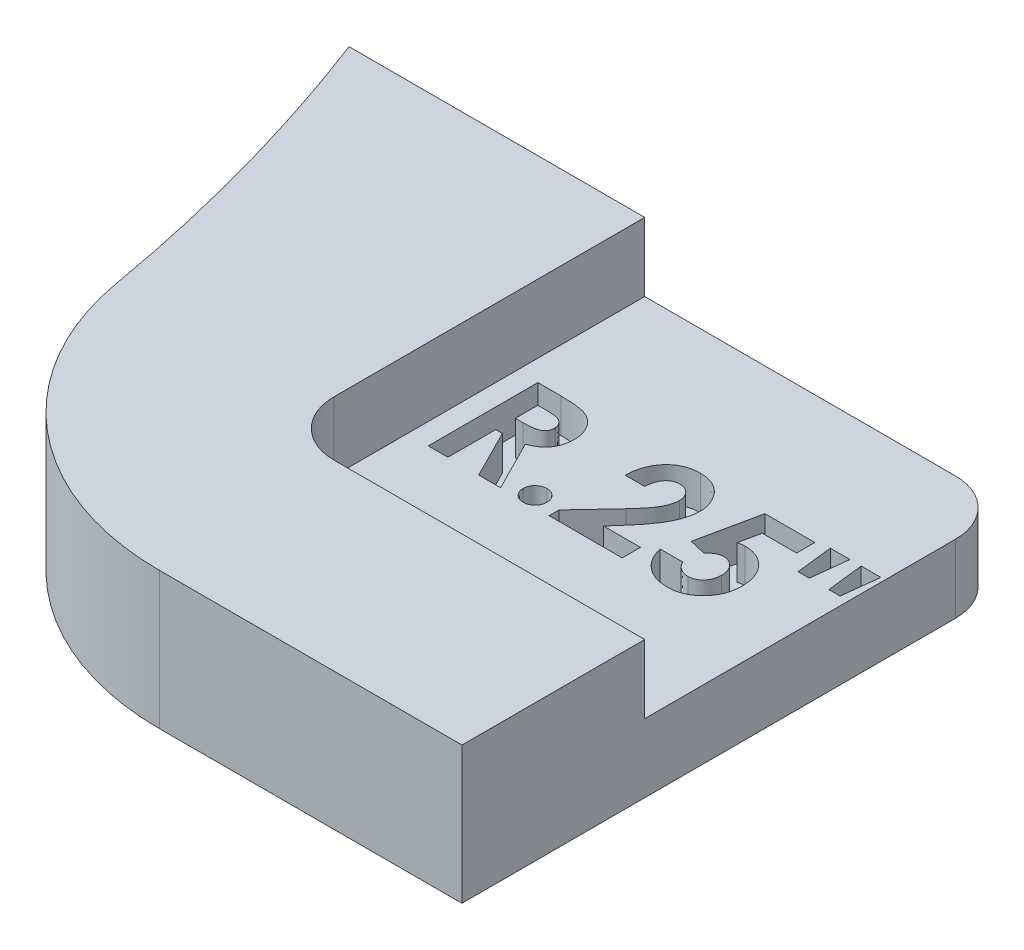
SolidWorks part; units mm, degrees
ref_plane "Front Plane" through (0, 0, 0) normal (0, 0, 1) x (1, 0, 0)
ref_plane "Top Plane" through (0, 0, 0) normal (0, 1, 0) x (1, 0, 0)
ref_plane "Right Plane" through (0, 0, 0) normal (1, 0, 0) x (0, 0, -1)
sketch "Sketch2" plane through (0, 0, 0) normal (0, 1, 0) x (1, 0, 0)
  line L0 (39.9034, 0) -> (66.5271, 0) construction
  line L4 (39.8718, 1.5875) -> (52.5718, 1.5875)
  line L5 (52.5718, 1.5875) -> (52.5718, 14.2875)
  line L6 (52.5718, 14.2875) -> (37.2579, 14.2875)
  arc A0 (39.8718, 1.5875) -> (37.2579, 14.2875) centre (0, 0) ccw
  arc A1 (37.2579, 14.2875) -> (-39.9034, 0) centre (0, 0) ccw construction
  arc A2 (-39.9034, 0) -> (39.9034, 0) centre (0, 0) ccw construction
  arc A3 (39.9034, 0) -> (39.8718, 1.5875) centre (0, 0) ccw construction
  point P6 (45.8249, 5.2638)
  point P7 (37.9479, 12.3384)
  point P10 (43.0639, 5.8161)
extrude "Boss-Extrude1" add sketch "Sketch2" along normal mid plane 3.175
fillet "Fillet1" radius 6.35 1 edges at (39.8718, 0, -1.5875)
sketch "Sketch3" plane through (0, 1.5875, 0) normal (0, 1, 0) x (1, 0, 0)
  line L1 (52.5718, 14.2875) -> (44.1051, 14.2875)
  line L2 (52.5718, 14.2875) -> (52.5718, 5.8208)
  line L3 (52.5718, 5.8208) -> (44.1051, 5.8208)
  line L4 (44.1051, 14.2875) -> (44.1051, 5.8208)
  dimension "D1" = 8.4667
extrude "Cut-Extrude1" cut sketch "Sketch3" against normal blind 1.5875
sketch "Sketch4" plane through (0, 0, 0) normal (0, 1, 0) x (1, 0, 0)
  line L0 (44.1051, 10.0542) -> (52.5718, 10.0542) construction
  line L1 (44.1051, 14.2875) -> (44.1051, 5.8208) construction
  line L2 (52.5718, 5.8208) -> (52.5718, 14.2875) construction
  line L3 (44.1051, 8.7842) -> (52.5718, 8.7842) construction
  text T0 "<b>R.25\"</b>\r\n<b> </b>" font "Century Gothic" height 2.54
  dimension "D1" = 1.27
extrude "Cut-Extrude2" cut sketch "Sketch4" against normal blind 0.7937
fillet "Fillet2" radius 1.27 2 edges at (44.1051, 0.7937, -5.8208) (52.5718, -0.7937, -14.2875)
equation "\"AIRFRAME_OD\"= 3.142in"
equation "\"AIRFRAME_ID\"= 3.00in"
equation "\"FLAT_T\"= 0.125in"
equation "\"NOSE_EXP_L\"= 3.5in"
equation "\"NOSE_SHOULDER_L\"= 5in"
equation "\"MAIN_L\"= 30in"
equation "\"RECO_COUP_L\"= 6in"
equation "\"RECO_SWITCH_L\"= 1.5in"
equation "\"DROGUE_L\"= 14in"
equation "\"ATS_FORE_COUP_L\"= 4in"
equation "\"ATS_AFT_COUP_L\"= 2.5in"
equation "\"LOWER_L\"= 16in"
equation "\"FIN_N\"= 4"
equation "\"CR_AFT_X\"= 0.5in"
equation "\"CR_FORE_X\"= 6in"
equation "\"D1@Sketch2\"=\"AIRFRAME_OD\""
equation "\"D2@Sketch2\"=\"FLAT_T\"/2"
equation "\"D1@Boss-Extrude1\"=\"FLAT_T\""
